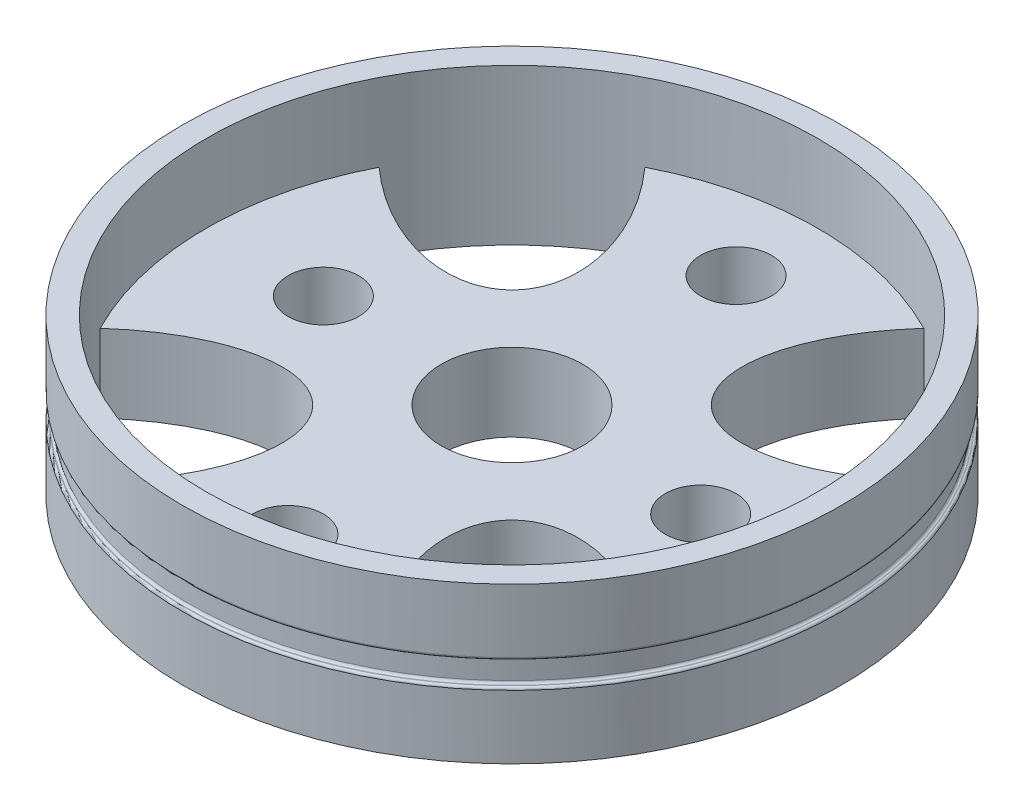
SolidWorks part; units mm, degrees
ref_plane "Front Plane" through (0, 0, 0) normal (0, 0, 1) x (1, 0, 0)
ref_plane "Top Plane" through (0, 0, 0) normal (0, 1, 0) x (1, 0, 0)
ref_plane "Right Plane" through (0, 0, 0) normal (1, 0, 0) x (0, 0, -1)
sketch "Sketch1" plane through (0, 0, 0) normal (0, 1, 0) x (1, 0, 0)
  circle A0 centre (0, 0) radius 13.975
  point P3 (0, -13.975)
  dimension "D1" = 27.95
extrude "Boss-Extrude1" add sketch "Sketch1" along normal blind 6.6
sketch "Sketch2" plane through (0, 6.6, 0) normal (0, 1, 0) x (1, 0, 0)
  circle A0 centre (0, 0) radius 12.975
  circle A1 centre (0, 0) radius 13.975 construction
  dimension "D1" = 1
extrude "Cut-Extrude1" cut sketch "Sketch2" against normal blind 3.3
ref_plane "Plane1" through (0, 0, 13.975) normal (0, 0, 1) x (1, 0, 0)
sketch "Sketch3" plane through (0, 0, 13.975) normal (0, 0, 1) x (1, 0, 0)
  line L0 (0, 0) -> (0, 6.6) construction
  line L1 (13.975, 6.6) -> (-13.975, 6.6) construction
  point P5 (0, 3.3)
ref_plane "Plane2" through (0, 3.3, 13.975) normal (0, 1, 0) x (1, 0, 0)
sketch "Sketch4" plane through (0, 3.3, 13.975) normal (0, 1, 0) x (1, 0, 0)
  circle A0 centre (0, 13.975) radius 13.975
  circle A1 centre (0, 13.975) radius 13.75
  dimension "D1" = 27.5
  dimension "D2" = 27.95
extrude "Cut-Extrude2" cut sketch "Sketch4" against normal blind 0.5 and the other way blind 0.5
fillet "Fillet1" radius 0.1 4 edges at (-13.975, 3.8, 0) (-13.975, 2.8, 0) (-13.75, 2.8, 0) (-13.75, 3.8, 0)
sketch "Sketch5" plane through (0, 3.3, 0) normal (0, 1, 0) x (1, 0, 0)
  line L0 (0, 0) -> (8, 0) construction
  line L1 (0, 9.5) -> (0, 0) construction
  line L2 (9.1747, 9.1747) -> (0, 0) construction
  line L3 (12.0031, 6.3463) -> (6.3463, 12.0031) construction
  circle A0 centre (0, 0) radius 3
  circle A2 centre (8, 0) radius 1.5
  circle A3 centre (0, 9.5) radius 1.5
  circle A4 centre (0, -9.5) radius 1.5
  circle A5 centre (-8, 0) radius 1.5
  circle A6 centre (0, 0) radius 12.975 construction
  arc A7 (11.5486, -5.9145) -> (5.9145, -11.5486) centre (0, 0) cw
  circle A8 centre (0, 0) radius 12.975
  arc A9 (-5.9145, -11.5486) -> (-11.5486, -5.9145) centre (0, 0) cw
  arc A10 (-11.5486, 5.9145) -> (-5.9145, 11.5486) centre (0, 0) cw
  arc A11 (5.9145, 11.5486) -> (11.5486, 5.9145) centre (0, 0) cw
  ellipse E0 centre (9.1747, 9.1747) end of major axis (4.225, 4.225) minor radius 4 (5.9145, 11.5486) -> (11.5486, 5.9145) ccw
  ellipse E1 centre (9.1747, -9.1747) end of major axis (14.1245, -14.1245) minor radius 4 (11.5486, -5.9145) -> (5.9145, -11.5486) ccw
  ellipse E2 centre (-9.1747, -9.1747) end of major axis (-14.1245, -14.1245) minor radius 4 (-5.9145, -11.5486) -> (-11.5486, -5.9145) ccw
  ellipse E3 centre (-9.1747, 9.1747) end of major axis (-14.1245, 14.1245) minor radius 4 (-11.5486, 5.9145) -> (-5.9145, 11.5486) ccw
  point P47 (0, 0)
  dimension "D1" = 6
  dimension "D2" = 3
  dimension "D8" = 25.95
  dimension "D3" = 8
  dimension "D4" = 9.5
  dimension "D5" = 7
  dimension "D6" = 4
  dimension "D7" = 45
  dimension "D9" = 4
extrude "Cut-Extrude4" cut sketch "Sketch5" against normal up to surface (3.3 mm away) contours A3 | A5 | A2 | A4 | E2 A9 | E3 A10 | E0 A11 | E1 A7 | A0 up to face at (0, 0, 13.975)
